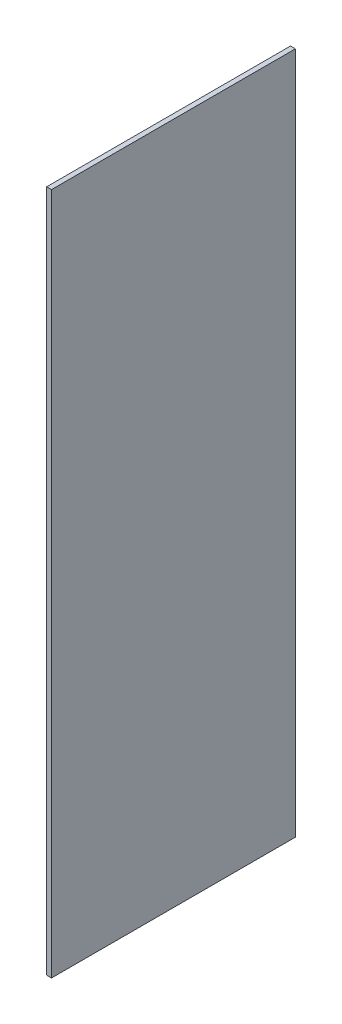
SolidWorks part; units mm, degrees
ref_plane "Front Plane" through (0, 0, 0) normal (0, 0, 1) x (1, 0, 0)
ref_plane "Top Plane" through (0, 0, 0) normal (0, 1, 0) x (1, 0, 0)
ref_plane "Right Plane" through (0, 0, 0) normal (1, 0, 0) x (0, 0, -1)
sketch "Sketch1" plane through (0, 0, 0) normal (0, 0, 1) x (1, 0, 0)
  line L1 (0, 0) -> (0.1, 0)
  line L2 (0, 0) -> (0, 14)
  line L3 (0, 14) -> (0.1, 14)
  line L4 (0.1, 0) -> (0.1, 14)
  dimension "D2" = 0.1
extrude "Boss-Extrude1" add sketch "Sketch1" along normal blind 5
equation "\"A.L\"= 0.07m"
equation "\"A.h\"= 0.007m"
equation "\"A.d\"= 0.005m"
equation "\"A.delta\"= 45.0001"
equation "\"A.w\"= 0m"
equation "\"A.v\"= 0.013m"
equation "\"A.s\"= 0.014m"
equation "\"A.t\"= 0.007m"
equation "\"B.L\"= 0.065m"
equation "\"B.h\"= 0.008m"
equation "\"B.s\"= 0.016m"
equation "\"B.t\"= 0.008m"
equation "\"C.h\"= 0.0065m"
equation "\"C.d\"= 0.005m"
equation "\"C.L\"= 0.05m"
equation "\"C.wmax\"= 0.003m"
equation "\"D.L\"= 0.06m"
equation "\"D.h\"= 0.008m"
equation "\"D.s\"= 0.012m"
equation "\"D.t\"= 0.008m"
equation "\"a_h\"= 0.0001m"
equation "\"a_d\"= 0.005m"
equation "\"a_L\"= 0.008m"
equation "\"b_h\"= 0.0004m"
equation "\"b_d\"= 0.005m"
equation "\"b_L\"= 0.007m"
equation "\"c_h\"= 0.0001m"
equation "\"c_d\"= 0.005m"
equation "\"c_L\"= 0.01m"
equation "\"d_h\"= 0.0001m"
equation "\"d_d\"= 0.005m"
equation "\"d_L\"= 0.01m"
equation "\"S.h\"= 0.015m"
equation "\"S.L\"= 0.09275m"
equation "\"D1@Sketch1\"=\"a_L\"+0.006"
equation "\"D2@Sketch1\"=\"a_h\""
equation "\"D1@Boss-Extrude1\"=\"a_d\""
